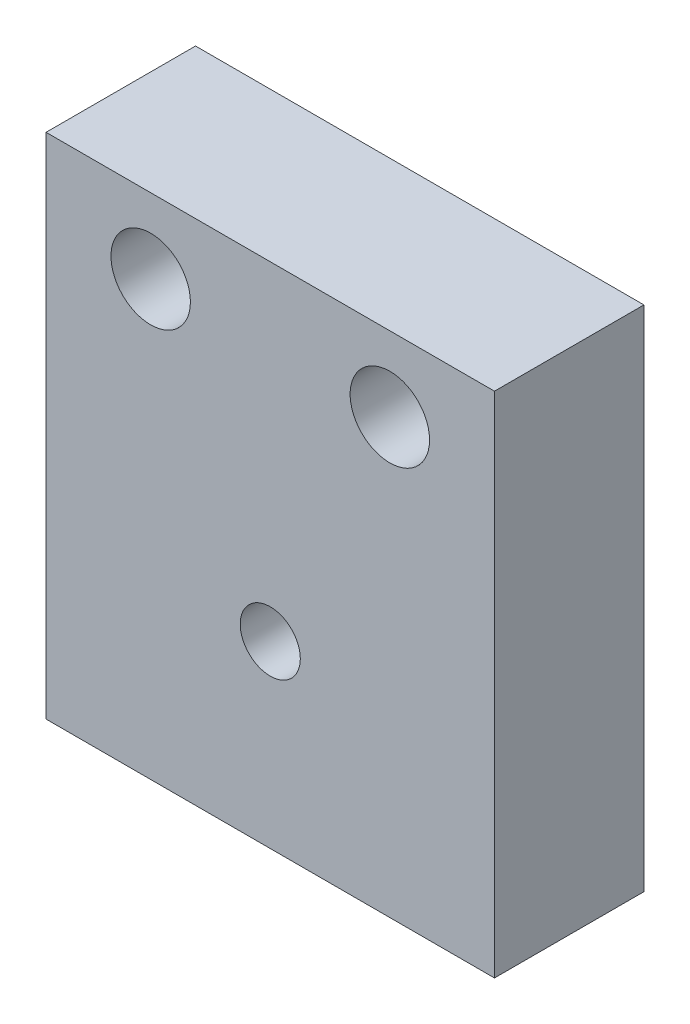
SolidWorks part; units mm, degrees
material "6063-T5"
ref_plane "Front Plane" through (0, 0, 0) normal (0, 0, 1) x (1, 0, 0)
ref_plane "Top Plane" through (0, 0, 0) normal (0, 1, 0) x (1, 0, 0)
ref_plane "Right Plane" through (0, 0, 0) normal (1, 0, 0) x (0, 0, -1)
sketch "Sketch1" plane through (0, 0, 0) normal (0, 0, 1) x (1, 0, 0)
  line L1 (0, 0) -> (38.1, 0)
  line L2 (0, 0) -> (0, 43.18)
  line L3 (0, 43.18) -> (38.1, 43.18)
  line L4 (38.1, 0) -> (38.1, 43.18)
  dimension "D1" = 38.1
  dimension "D2" = 43.18
extrude "Boss-Extrude1" add sketch "Sketch1" against normal blind 12.7
sketch "Sketch3" plane through (0, 0, 0) normal (0, 0, 1) x (1, 0, 0)
  line L0 (19.05, -987.2485) -> (19.05, 49012.7515) construction
  line L1 (0, 43.18) -> (0, 0) construction
  line L2 (38.1, 0) -> (38.1, 43.18) construction
  line L4 (38.1, 43.18) -> (0, 43.18) construction
  point P6 (19.05, 15.24)
  dimension "D1" = 27.94
sketch "Sketch5" plane through (0, 0, 0) normal (0, 0, 1) x (1, 0, 0)
  line L0 (19.05, -968.1712) -> (19.05, 49031.8288) construction
  line L1 (0, 43.18) -> (0, 0) construction
  line L2 (38.1, 0) -> (38.1, 43.18) construction
  line L3 (38.1, 43.18) -> (0, 43.18) construction
  point P6 (8.89, 36.83)
  point P7 (29.21, 36.83)
  dimension "D1" = 20.32
  dimension "D2" = 6.35
hole_wizard "17/64 (0.26563) Diameter Hole1" positions "3DSketch2" profile "Sketch7" hole size "17/64" standard "ANSI Inch" end condition through all
sketch3d "3DSketch2"
  point P0 (29.21, 36.83, 0)
  point P3 (8.89, 36.83, 0)
sketch "Sketch7" plane through (29.21, 36.83, 0) normal (1, 0, 0) x (0, -1, 0)
  line L0 (0, 0) -> (0, 12.7)
  line L1 (0, 12.7) -> (3.3735, 12.7)
  line L2 (3.3735, 12.7) -> (3.3735, 0)
  line L5 (3.3735, 0) -> (0, 0)
  line L11 (0, -6.35) -> (0, 107.95) construction
  dimension "Thru Hole Dia." = 6.747
  dimension "Thru Hole Depth" = 12.7
hole_wizard "1/4-20 Tapped Hole1" positions "Sketch8" profile "Sketch9" tap size "1/4-20" standard "ANSI Inch" end condition up to next
sketch "Sketch8" plane through (0, 0, 0) normal (0, 0, 1) x (1, 0, 0)
  point P0 (19.05, 15.24)
sketch "Sketch9" plane through (19.05, 15.24, 0) normal (1, 0, 0) x (0, -1, 0)
  line L0 (0, 0) -> (0, 12.7)
  line L1 (0, 12.7) -> (2.5527, 12.7)
  line L2 (2.5527, 12.7) -> (2.5527, 0)
  line L5 (2.5527, 0) -> (0, 0)
  line L11 (0, -6.35) -> (0, 107.95) construction
  dimension "Thru Tap Drill Dia." = 5.1054
  dimension "Thru Tap Drill Depth" = 12.7
cosmetic thread "Hole Thread1" parameters "D2"=6.35
